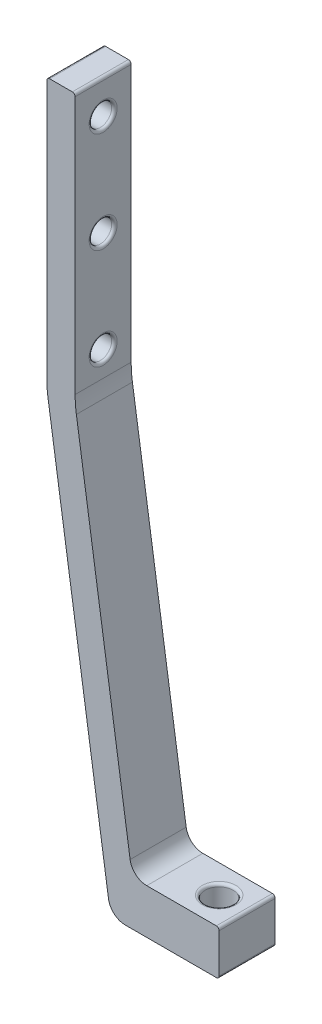
SolidWorks part; units mm, degrees
material "7075-T6 (SN)"
ref_plane "Front Plane" through (0, 0, 0) normal (0, 0, 1) x (1, 0, 0)
ref_plane "Top Plane" through (0, 0, 0) normal (0, 1, 0) x (1, 0, 0)
ref_plane "Right Plane" through (0, 0, 0) normal (1, 0, 0) x (0, 0, -1)
sketch "Sketch1" plane through (0, 0, 0) normal (0, 0, 1) x (1, 0, 0)
  line L0 (0, 0) -> (0, 42.8679) construction
  line L1 (-32, 0) -> (-32, 10.6264) construction
  line L2 (-27, 0) -> (-46.3566, 0)
  line L3 (-46.3566, 0) -> (-57.75, 76)
  line L5 (-52.6941, 76) -> (-42.5, 8)
  line L6 (-42.5, 8) -> (-27, 8)
  line L7 (-27, 8) -> (-27, 0)
  line L8 (-52.6941, 76) -> (-52.6941, 124)
  line L12 (-57.75, 76) -> (-57.75, 124)
  line L13 (-57.75, 124) -> (-52.6941, 124)
  dimension "D1" = 32
  dimension "D2" = 115.5
  dimension "D3" = 85
  dimension "D4" = 5
  dimension "D5" = 8
  dimension "D6" = 54
  dimension "D7" = 124
  dimension "D9" = 48
extrude "Boss-Extrude1" add sketch "Sketch1" along normal mid plane 10
sketch "Sketch3" plane through (0, 8, 0) normal (0, 1, 0) x (1, 0, 0)
  circle A0 centre (-32, 0) radius 2.5
  dimension "D1" = 5
extrude "Cut-Extrude1" cut sketch "Sketch3" against normal blind 10
sketch "Sketch4" plane through (-52.6941, 0, 0) normal (1, 0, 0) x (0, 0, -1)
  line L1 (-5, 124) -> (5, 124) construction
  circle A0 centre (0, 100) radius 2
  circle A1 centre (0, 82) radius 2
  circle A2 centre (0, 118) radius 2
  dimension "D1" = 4
  dimension "D2" = 18
  dimension "D3" = 18
  dimension "D4" = 6
extrude "Cut-Extrude2" cut sketch "Sketch4" against normal up to next
fillet "Fillet1" radius 3 2 edges at (-46.3566, 0, 0) (-42.5, 8, 0)
fillet "Fillet2" radius 0.5 12 edges at (-57.75, 100, -2) (-52.6941, 100, -2) (-34.5, 0, 0) (-32, 8, 2.5) (-52.6941, 82, -2) (-27, 0, 0) (-27, 8, 0) (-52.6941, 124, 0) (-57.75, 124, 0) (-57.75, 82, -2) (-57.75, 118, -2) (-52.6941, 118, -2)
fillet "Fillet3" radius 20 2 edges at (-57.75, 76, 0) (-52.6941, 76, 0)
